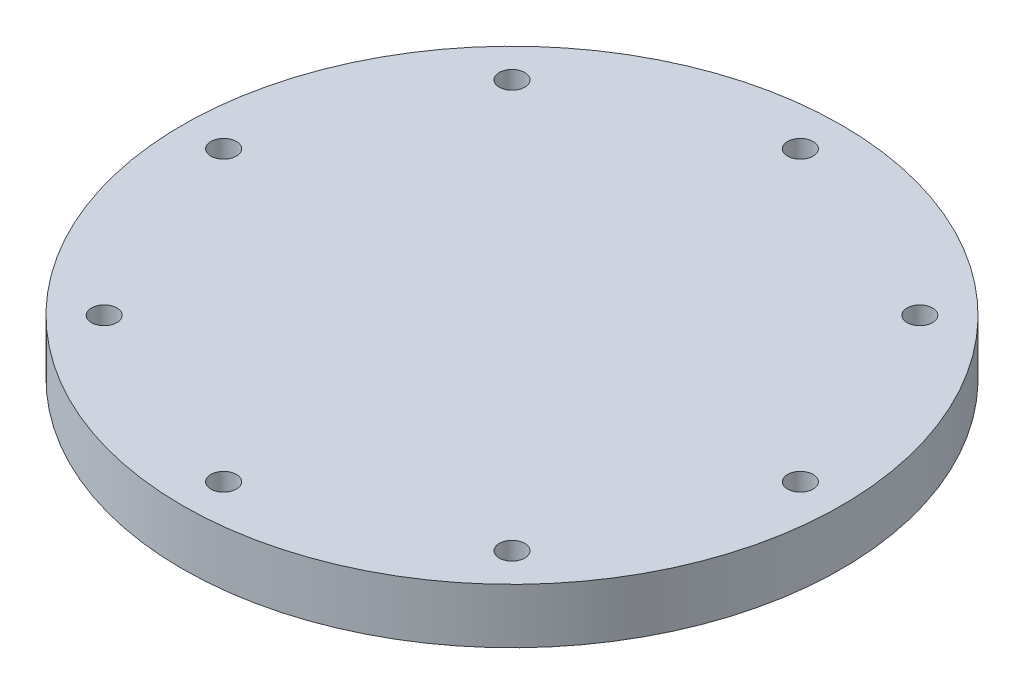
SolidWorks part; units mm, degrees
ref_plane "Front Plane" through (0, 0, 0) normal (0, 0, 1) x (1, 0, 0)
ref_plane "Top Plane" through (0, 0, 0) normal (0, 1, 0) x (1, 0, 0)
ref_plane "Right Plane" through (0, 0, 0) normal (1, 0, 0) x (0, 0, -1)
sketch "Sketch1" plane through (0, 0, 0) normal (0, 1, 0) x (1, 0, 0)
  circle A0 centre (0, 0) radius 38.1
  dimension "D1" = 76.2
extrude "Boss-Extrude1" add sketch "Sketch1" along normal blind 6.35
sketch "Sketch2" plane through (0, 0, 0) normal (0, -1, 0) x (1, 0, 0)
  circle A0 centre (0, 0) radius 33.3375
  circle A1 centre (0, 33.3375) radius 0.762
  dimension "D1" = 66.675
hole_wizard "CBORE for #4 Button Head Cap Screw1" positions "Sketch5" profile "Sketch4" counterbore size "#4" standard "ANSI Inch" end condition through all
sketch "Sketch5" plane through (0, 0, 0) normal (0, -1, 0) x (-1, 0, 0)
  point P0 (0, -33.3375)
sketch "Sketch4" plane through (0, 0, 33.3375) normal (1, 0, 0) x (0, 0, -1)
  line L0 (0, 0) -> (0, 6.35)
  line L1 (0, 6.35) -> (1.4732, 6.35)
  line L3 (1.4732, 6.35) -> (1.4732, 2.8448)
  line L4 (1.4732, 2.8448) -> (2.413, 2.8448)
  line L5 (2.413, 2.8448) -> (2.413, 0)
  line L7 (2.413, 0) -> (0, 0)
  line L11 (0, -6.35) -> (0, 107.95) construction
  dimension "Thru Hole Dia." = 2.9464
  dimension "Thru Hole Depth" = 6.35
  dimension "C'Bore Dia." = 4.826
  dimension "C'Bore Depth" = 2.8448
pattern_circular "CirPattern1" count 8 over 360 about axis through (0, 0, 0) along (0, 1, 0) of "CBORE for #4 Button Head Cap Screw1"
sketch "Sketch6" plane through (0, 6.35, 0) normal (0, 1, 0) x (1, 0, 0)
  circle A0 centre (0, 0) radius 28.575
  dimension "D1" = 57.15
